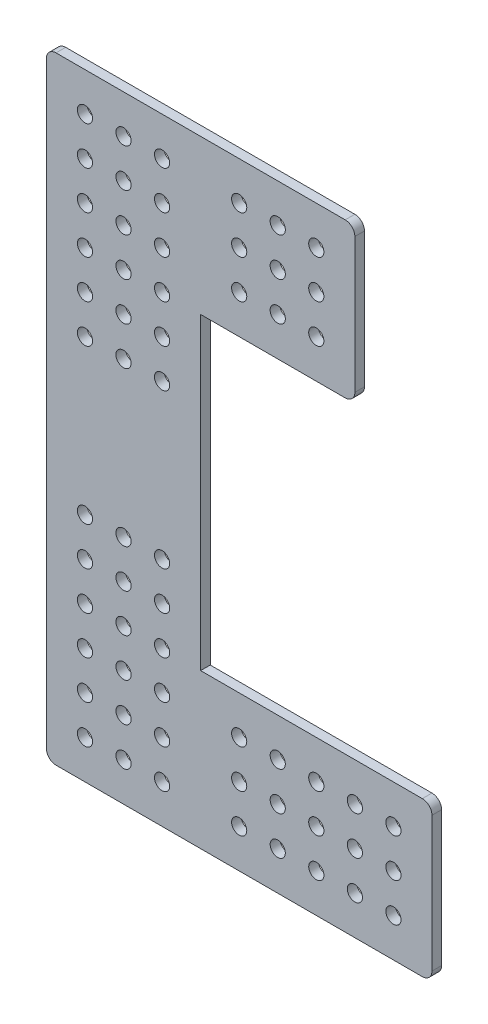
SolidWorks part; units mm, degrees
ref_plane "Front Plane" through (0, 0, 0) normal (0, 0, 1) x (1, 0, 0)
ref_plane "Top Plane" through (0, 0, 0) normal (0, 1, 0) x (1, 0, 0)
ref_plane "Right Plane" through (0, 0, 0) normal (1, 0, 0) x (0, 0, -1)
sketch "Sketch1" plane through (0, 0, 0) normal (0, 0, 1) x (1, 0, 0)
  line L0 (23.16, 167.0479) -> (26.335, 167.0479)
  line L1 (-24.465, 14.6479) -> (99.36, 14.6479)
  line L2 (-24.465, 14.6479) -> (-24.465, -32.9771)
  line L3 (-21.29, -36.1521) -> (99.36, -36.1521)
  line L4 (102.535, 11.4729) -> (102.535, -32.9771)
  line L5 (-21.29, 167.0479) -> (23.16, 167.0479)
  line L6 (-24.465, 163.8729) -> (-24.465, 14.6479)
  line L7 (-24.465, 14.6479) -> (26.335, 14.6479)
  line L8 (26.335, 163.8729) -> (26.335, 14.6479)
  line L9 (26.335, 167.0479) -> (26.335, 163.8729)
  arc A0 (-24.465, -32.9771) -> (-21.29, -36.1521) centre (-21.29, -32.9771) ccw
  arc A1 (99.36, -36.1521) -> (102.535, -32.9771) centre (99.36, -32.9771) ccw
  arc A2 (99.36, 14.6479) -> (102.535, 11.4729) centre (99.36, 11.4729) cw
  arc A4 (-21.29, 167.0479) -> (-24.465, 163.8729) centre (-21.29, 163.8729) ccw
  point P10 (-24.465, -36.1521)
  point P13 (102.535, -36.1521)
  point P16 (102.535, 14.6479)
  point P19 (26.335, 167.0479)
  point P22 (-24.465, 167.0479)
  dimension "D5" = 3.175
  dimension "D1" = 50.8
  dimension "D2" = 50.8
  dimension "D3" = 127
  dimension "D4" = 152.4
extrude "Boss-Extrude1" add sketch "Sketch1" along normal blind 3.175 contours L8 L5 L6 L1 | L4 L1 L2 L3
sketch "Sketch2" plane through (0, 0, 3.175) normal (0, 0, 1) x (1, 0, 0)
  line L0 (-24.465, 163.8729) -> (-24.465, -32.9771) construction
  line L1 (-21.29, 167.0479) -> (26.335, 167.0479) construction
  line L2 (102.535, 11.4729) -> (102.535, -32.9771) construction
  line L3 (-21.29, -36.1521) -> (99.36, -36.1521) construction
  circle A0 centre (-11.765, 154.3479) radius 2.5
  circle A1 centre (89.835, -23.4521) radius 2.5
  circle A2 centre (0.935, 154.3479) radius 2.5
  circle A3 centre (13.635, 154.3479) radius 2.5
  circle A4 centre (0.935, 141.6479) radius 2.5
  circle A5 centre (13.635, 141.6479) radius 2.5
  circle A6 centre (0.935, 128.9479) radius 2.5
  circle A7 centre (13.635, 128.9479) radius 2.5
  circle A8 centre (0.935, 116.2479) radius 2.5
  circle A9 centre (13.635, 116.2479) radius 2.5
  circle A10 centre (0.935, 103.5479) radius 2.5
  circle A11 centre (13.635, 103.5479) radius 2.5
  circle A12 centre (0.935, 90.8479) radius 2.5
  circle A13 centre (13.635, 90.8479) radius 2.5
  circle A20 centre (-11.765, 141.6479) radius 2.5
  circle A21 centre (-11.765, 128.9479) radius 2.5
  circle A22 centre (-11.765, 116.2479) radius 2.5
  circle A23 centre (-11.765, 103.5479) radius 2.5
  circle A24 centre (-11.765, 90.8479) radius 2.5
  circle A28 centre (77.135, -23.4521) radius 2.5
  circle A29 centre (64.435, -23.4521) radius 2.5
  circle A30 centre (51.735, -23.4521) radius 2.5
  circle A31 centre (39.035, -23.4521) radius 2.5
  circle A33 centre (77.135, -10.7521) radius 2.5
  circle A34 centre (64.435, -10.7521) radius 2.5
  circle A35 centre (51.735, -10.7521) radius 2.5
  circle A36 centre (39.035, -10.7521) radius 2.5
  circle A38 centre (77.135, 1.9479) radius 2.5
  circle A39 centre (64.435, 1.9479) radius 2.5
  circle A40 centre (51.735, 1.9479) radius 2.5
  circle A41 centre (39.035, 1.9479) radius 2.5
  circle A43 centre (89.835, -10.7521) radius 2.5
  circle A44 centre (89.835, 1.9479) radius 2.5
  circle A45 centre (-11.765, 40.0479) radius 2.5
  circle A46 centre (0.935, 40.0479) radius 2.5
  circle A47 centre (13.635, 40.0479) radius 2.5
  circle A48 centre (-11.765, 27.3479) radius 2.5
  circle A49 centre (0.935, 27.3479) radius 2.5
  circle A50 centre (13.635, 27.3479) radius 2.5
  circle A51 centre (-11.765, 14.6479) radius 2.5
  circle A52 centre (0.935, 14.6479) radius 2.5
  circle A53 centre (13.635, 14.6479) radius 2.5
  circle A54 centre (-11.765, 1.9479) radius 2.5
  circle A55 centre (0.935, 1.9479) radius 2.5
  circle A56 centre (13.635, 1.9479) radius 2.5
  circle A57 centre (-11.765, -10.7521) radius 2.5
  circle A58 centre (0.935, -10.7521) radius 2.5
  circle A59 centre (13.635, -10.7521) radius 2.5
  circle A60 centre (-11.765, -23.4521) radius 2.5
  circle A61 centre (0.935, -23.4521) radius 2.5
  circle A62 centre (13.635, -23.4521) radius 2.5
  circle A63 centre (26.335, -23.4521) radius 2.5 [skipped]
  circle A64 centre (26.335, -10.7521) radius 2.5 [skipped]
  circle A65 centre (26.335, 1.9479) radius 2.5 [skipped]
  circle A66 centre (0.935, 78.1479) radius 2.5 [skipped]
  circle A67 centre (13.635, 78.1479) radius 2.5 [skipped]
  circle A68 centre (0.935, 65.4479) radius 2.5 [skipped]
  circle A69 centre (13.635, 65.4479) radius 2.5 [skipped]
  circle A70 centre (0.935, 52.7479) radius 2.5 [skipped]
  circle A71 centre (13.635, 52.7479) radius 2.5 [skipped]
  circle A72 centre (-11.765, 78.1479) radius 2.5 [skipped]
  circle A73 centre (-11.765, 65.4479) radius 2.5 [skipped]
  circle A74 centre (-11.765, 52.7479) radius 2.5 [skipped]
  dimension "D1" = 5
  dimension "D4" = 5
  dimension "D2" = 12.7
  dimension "D3" = 12.7
  dimension "D5" = 12.7
  dimension "D6" = 12.7
  dimension "D7" = 3
  dimension "D9" = 15
  dimension "D8" = 6
extrude "Cut-Extrude1" cut sketch "Sketch2" against normal through all
sketch "Sketch3" plane through (0, 0, 3.175) normal (0, 0, 1) x (1, 0, 0)
  line L0 (26.335, 167.0479) -> (26.335, 14.6479) construction
  line L1 (73.96, 167.0479) -> (26.335, 167.0479)
  line L2 (77.135, 163.8729) -> (77.135, 119.4229)
  line L3 (73.96, 116.2479) -> (26.335, 116.2479)
  line L4 (26.335, 167.0479) -> (26.335, 116.2479)
  line L5 (-21.29, 167.0479) -> (26.335, 167.0479) construction
  arc A0 (77.135, 119.4229) -> (73.96, 116.2479) centre (73.96, 119.4229) cw
  arc A1 (73.96, 167.0479) -> (77.135, 163.8729) centre (73.96, 163.8729) cw
  point P10 (77.135, 116.2479)
  point P13 (77.135, 167.0479)
  dimension "D3" = 3.175
  dimension "D1" = 50.8
  dimension "D2" = 50.8
extrude "Boss-Extrude2" add sketch "Sketch3" against normal up to surface (3.175 mm away) up to face at (66.935, -10.7521, 0)
sketch "Sketch4" plane through (0, 0, 3.175) normal (0, 0, 1) x (1, 0, 0)
  line L0 (77.135, 119.4229) -> (77.135, 163.8729) construction
  line L1 (-21.29, 167.0479) -> (73.96, 167.0479) construction
  circle A0 centre (64.435, 154.3479) radius 2.505
  circle A1 centre (51.735, 154.3479) radius 2.505
  circle A2 centre (39.035, 154.3479) radius 2.505
  circle A4 centre (51.735, 141.6479) radius 2.505
  circle A5 centre (39.035, 141.6479) radius 2.505
  circle A7 centre (51.735, 128.9479) radius 2.505
  circle A8 centre (39.035, 128.9479) radius 2.505
  circle A10 centre (64.435, 141.6479) radius 2.505
  circle A11 centre (64.435, 128.9479) radius 2.505
  circle A12 centre (26.335, 154.3479) radius 2.505 [skipped]
  circle A13 centre (26.335, 141.6479) radius 2.505 [skipped]
  circle A14 centre (26.335, 128.9479) radius 2.505 [skipped]
  dimension "D1" = 5.01
  dimension "D2" = 12.7
  dimension "D3" = 12.7
  dimension "D4" = 4
extrude "Cut-Extrude2" cut sketch "Sketch4" against normal through all
